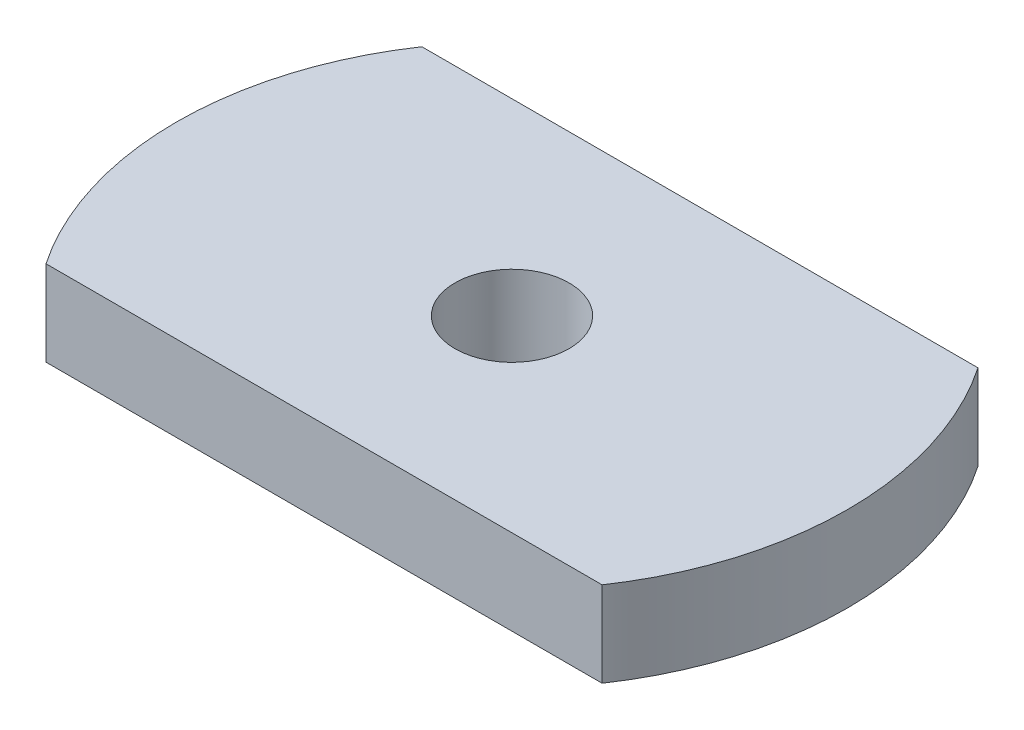
SolidWorks part; units mm, degrees
material "Liga de aço (SS)"
ref_plane "Plano frontal" through (0, 0, 0) normal (0, 0, 1) x (1, 0, 0)
ref_plane "Plano superior" through (0, 0, 0) normal (0, 1, 0) x (1, 0, 0)
ref_plane "Plano direito" through (0, 0, 0) normal (1, 0, 0) x (0, 0, -1)
sketch "Esboço1" plane through (0, 0, 0) normal (0, 1, 0) x (1, 0, 0)
  line L0 (0, 0) -> (0, 21463.0573) construction
  line L1 (0, 0) -> (21463.0573, 0) construction
  line L2 (-20.7123, 14) -> (20.7123, 14)
  line L3 (-20.7123, -14) -> (20.7123, -14)
  arc A0 (-20.7123, 14) -> (-20.7123, -14) centre (0, 0) ccw
  arc A1 (20.7123, -14) -> (20.7123, 14) centre (0, 0) ccw
  circle A2 centre (0, 0) radius 4.25
  dimension "D1" = 25
  dimension "D3" = 8.5
  dimension "D2" = 28
extrude "Ressalto-extrusão1" add sketch "Esboço1" along normal blind 6.35
